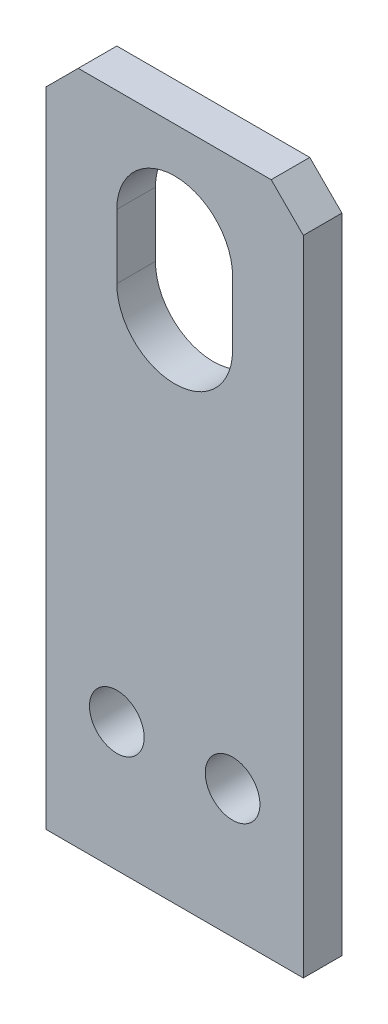
SolidWorks part; units mm, degrees
other "Camera1"
material "PA Type 6"
ref_plane "Front Plane" through (0, 0, 0) normal (0, 0, 1) x (1, 0, 0)
ref_plane "Top Plane" through (0, 0, 0) normal (0, 1, 0) x (1, 0, 0)
ref_plane "Right Plane" through (0, 0, 0) normal (1, 0, 0) x (0, 0, -1)
sketch "Sketch1" plane through (0, 0, 0) normal (0, 0, 1) x (1, 0, 0)
  line L0 (0, -1000) -> (0, 49000) construction
  line L1 (20, -52.5) -> (-20, -52.5)
  line L2 (20, -52.5) -> (20, 52.5)
  line L3 (20, 52.5) -> (-20, 52.5)
  line L4 (-20, -52.5) -> (-20, 52.5)
  line L5 (20, -52.5) -> (-20, 52.5) construction
  line L6 (20, 52.5) -> (-20, -52.5) construction
  line L7 (0, 36.5) -> (0, 26.5) construction
  line L8 (9, 36.5) -> (9, 26.5)
  line L9 (-9, 36.5) -> (-9, 26.5)
  arc A0 (9, 36.5) -> (-9, 36.5) centre (0, 36.5) ccw
  arc A1 (-9, 26.5) -> (9, 26.5) centre (0, 26.5) ccw
  circle A2 centre (9, -32.5) radius 4.25
  circle A3 centre (-9, -32.5) radius 4.25
  point P0 (0, 0)
  point P10 (0, 31.5)
  point P19 (0, 17.5)
  dimension "D4" = 8.5
  dimension "D1" = 40
  dimension "D2" = 105
  dimension "D3" = 18
  dimension "D5" = 20
  dimension "D6" = 18
  dimension "D7" = 10
  dimension "D8" = 70
extrude "Boss-Extrude1" add sketch "Sketch1" along normal mid plane 6
chamfer "Chamfer1" distance 5 angle 45 2 edges at (-20, 52.5, 0) (20, 52.5, 0)
